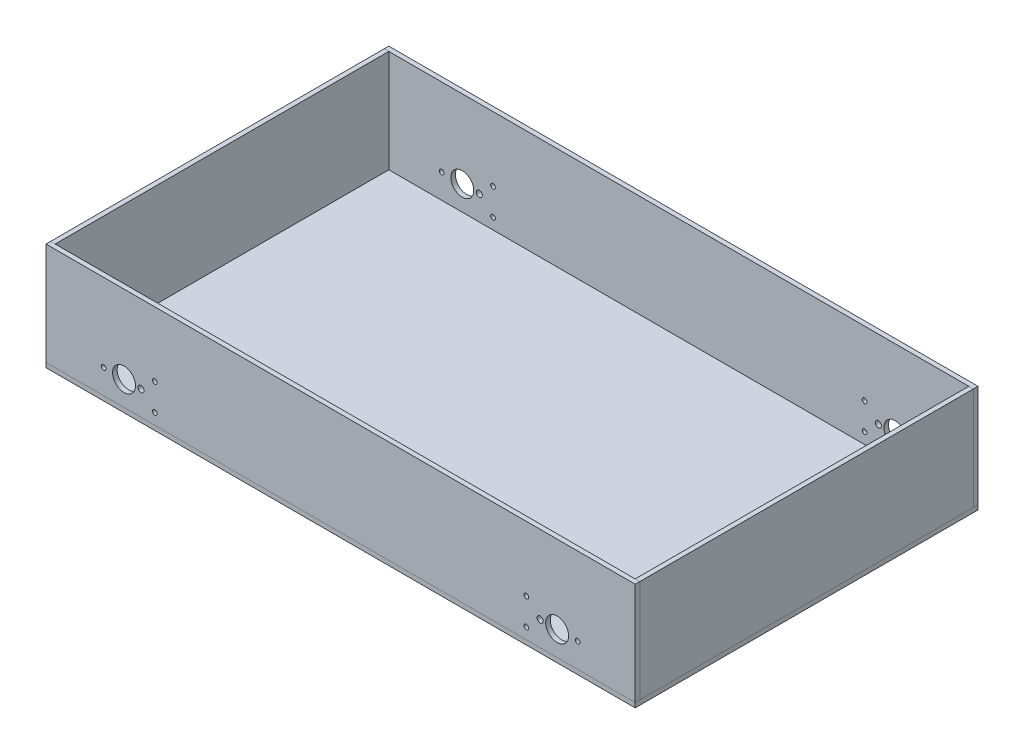
SolidWorks part; units mm, degrees
material "Arce"
ref_plane "Alzado" through (0, 0, 0) normal (0, 0, 1) x (1, 0, 0)
ref_plane "Planta" through (0, 0, 0) normal (0, 1, 0) x (1, 0, 0)
ref_plane "Vista lateral" through (0, 0, 0) normal (1, 0, 0) x (0, 0, -1)
sketch "Croquis1" plane through (0, 0, 0) normal (0, 1, 0) x (1, 0, 0)
  line L1 (192.5, 112) -> (-192.5, 112)
  line L2 (192.5, 112) -> (192.5, -112)
  line L3 (192.5, -112) -> (-192.5, -112)
  line L4 (-192.5, 112) -> (-192.5, -112)
  line L5 (192.5, 112) -> (-192.5, -112) construction
  line L6 (192.5, -112) -> (-192.5, 112) construction
  point P0 (0, 0)
  dimension "D1" = 224
  dimension "D2" = 385
extrude "Saliente-Extruir1" add sketch "Croquis1" along normal blind 3
sketch "Croquis3" plane through (0, 3, 0) normal (0, 1, 0) x (1, 0, 0)
  line L0 (192.5, -112) -> (192.5, 112) construction
  line L1 (-192.5, 112) -> (192.5, 112)
  line L2 (-192.5, 112) -> (-192.5, 109)
  line L3 (-192.5, 109) -> (192.5, 109)
  line L4 (192.5, 112) -> (192.5, 109)
  line L6 (-192.5, -112) -> (192.5, -112)
  line L7 (-192.5, -112) -> (-192.5, -109)
  line L8 (-192.5, -109) -> (192.5, -109)
  line L9 (192.5, -112) -> (192.5, -109)
  dimension "D1" = 3
  dimension "D2" = 3
extrude "Saliente-Extruir2" add sketch "Croquis3" along normal blind 67 separate body
sketch "Croquis4" plane through (0, 3, 0) normal (0, 1, 0) x (1, 0, 0)
  line L0 (192.5, -109) -> (-192.5, -109) construction
  line L1 (-192.5, 109) -> (-189.5, 109)
  line L2 (-192.5, 109) -> (-192.5, -109)
  line L3 (-192.5, -109) -> (-189.5, -109)
  line L4 (-189.5, 109) -> (-189.5, -109)
  line L6 (192.5, 109) -> (189.5, 109)
  line L7 (192.5, 109) -> (192.5, -109)
  line L8 (192.5, -109) -> (189.5, -109)
  line L9 (189.5, 109) -> (189.5, -109)
  dimension "D1" = 3
  dimension "D2" = 3
extrude "Saliente-Extruir3" add sketch "Croquis4" along normal blind 67 separate body
sketch "Croquis5" plane through (0, 0, 112) normal (0, 0, 1) x (1, 0, 0)
  line L0 (-141.5, 19) -> (141.5, 19) construction
  line L1 (-192.5, 70) -> (-192.5, 3) construction
  line L2 (-192.5, 70) -> (192.5, 70) construction
  line L3 (-155.2119, 61.86) -> (-4.5706, 110.0537) construction
  line L4 (-141.5, -26) -> (141.5, -26) construction
  line L5 (4.5706, 110.0537) -> (155.2119, 61.86)
  line L6 (0, 95.767) -> (0, 19) construction
  line L7 (-121.4, 27.75) -> (-121.4, 10.25) construction
  line L8 (-195.0167, 72.0222) -> (196.4626, 72.0222)
  line L9 (-195.0167, 72.0222) -> (-195.0167, -26.3884)
  line L10 (-195.0167, -26.3884) -> (196.4626, -26.3884)
  line L11 (196.4626, 72.0222) -> (196.4626, -26.3884)
  line L12 (-121.4, 19) -> (-141.5, 19) construction
  line L13 (121.4, 27.75) -> (121.4, 10.25) construction
  line L14 (121.4, 19) -> (141.5, 19) construction
  line L15 (-141.5, 19) -> (-154.9, 19) construction
  line L16 (141.5, 19) -> (154.9, 19) construction
  line L17 (-88, 30.15) -> (-88, 7.85)
  line L18 (-88, 7.85) -> (-152.4, 7.85)
  line L19 (-152.4, 7.85) -> (-152.4, 30.15)
  line L20 (-152.4, 30.15) -> (-88, 30.15)
  circle A0 centre (-141.5, 19) radius 7.5
  circle A1 centre (141.5, 19) radius 7.5
  circle A2 centre (-141.5, 19) radius 45 construction
  circle A3 centre (141.5, 19) radius 45 construction
  circle A4 centre (0, 95.767) radius 15 construction
  circle A5 centre (-121.4, 10.25) radius 1.55
  circle A6 centre (-121.4, 27.75) radius 1.55
  circle A7 centre (121.4, 27.75) radius 1.55
  circle A8 centre (121.4, 10.25) radius 1.55
  circle A9 centre (-154.9, 19) radius 1.55
  circle A10 centre (154.9, 19) radius 1.55
  arc A11 (-147.4, 30.15) -> (-152.4, 25.15) centre (-147.4, 25.15) ccw
  arc A12 (-147.4, 7.85) -> (-152.4, 12.85) centre (-147.4, 12.85) cw
  circle A13 centre (-130.4, 19) radius 2
  circle A14 centre (130.4, 19) radius 2
  point P4 (0, 19)
  point P51 (-141.5, 19)
  dimension "D1" = 15
  dimension "D3" = 90
  dimension "D5" = 30
  dimension "D6" = 3.1
  dimension "D15" = 5
  dimension "D17" = 4
  dimension "D18" = 4
  dimension "D2" = 51
  dimension "D4" = 51
  dimension "D7" = 17.5
  dimension "D8" = 17.5
  dimension "D9" = 20.1
  dimension "D10" = 13.4
  dimension "D11" = 31
  dimension "D12" = 64.4
  dimension "D13" = 22.3
  dimension "D14" = 11.15
  dimension "D16" = 9
  dimension "D19" = 9
extrude "Cortar-Extruir1" cut sketch "Croquis5" against normal up to surface (224 mm away) contours A0 | A1 | A6 | A5 | A9 | A7 | A8 | A10 | A13 | A14 up to face at (0, 36.5, -112)
equation "\"D1@Croquis1\"    = \"Ancho Caja Gen\"-((\"Grosor madera\"+\"Grosor de Llanta\")*2)"
equation "\"D1@Saliente-Extruir1\"=\"Grosor madera\""
equation "\"D1@Saliente-Extruir2\"=\"AlturaP\"-\"Grosor madera\""
equation "\"D1@Saliente-Extruir3\"=\"AlturaP\"-\"Grosor madera\""
equation "\"D2@Croquis5\"=(\"Grosor madera\"*2)+(\"Diametro llanta\"/2)"
equation "\"D3@Croquis5\"=\"Diametro llanta\""
